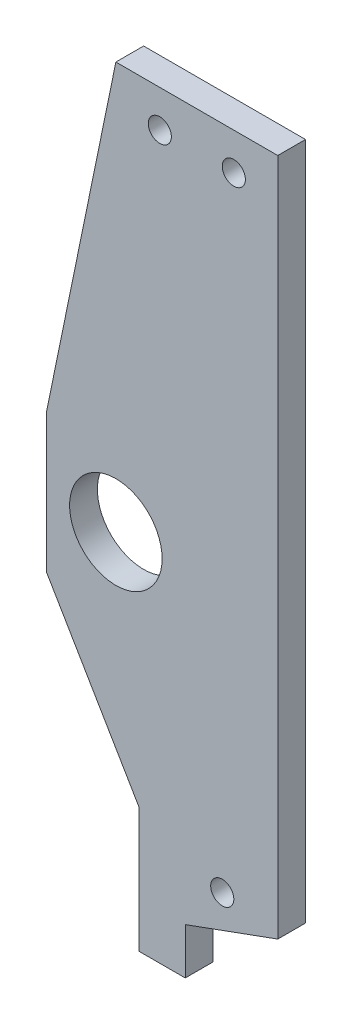
SolidWorks part; units mm, degrees
ref_plane "Front Plane" through (0, 0, 0) normal (0, 0, 1) x (1, 0, 0)
ref_plane "Top Plane" through (0, 0, 0) normal (0, 1, 0) x (1, 0, 0)
ref_plane "Right Plane" through (0, 0, 0) normal (1, 0, 0) x (0, 0, -1)
sketch "Sketch1" plane through (0, 0, 0) normal (0, 0, 1) x (1, 0, 0)
  line L1 (-33.1101, -53.4588) -> (-23.1101, -53.4588)
  line L2 (-33.1101, -53.4588) -> (-33.1101, 23.5412)
  line L3 (-33.1101, 23.5412) -> (-23.1101, 23.5412)
  line L4 (-23.1101, -53.4588) -> (-23.1101, 23.5412)
  dimension "D1" = 77
  dimension "D2" = 10
extrude "Boss-Extrude1" add sketch "Sketch1" along normal blind 3
sketch "Sketch2" plane through (0, 0, 3) normal (0, 0, 1) x (1, 0, 0)
  line L0 (-33.1101, 23.5412) -> (-33.1101, -53.4588) construction
  line L1 (-33.1101, -27.9588) -> (-48.1101, -27.9588)
  line L2 (-33.1101, -27.9588) -> (-33.1101, -12.9588)
  line L3 (-33.1101, -12.9588) -> (-48.1101, -12.9588)
  line L4 (-48.1101, -27.9588) -> (-48.1101, -12.9588)
  line L5 (-33.1101, -53.4588) -> (-23.1101, -53.4588) construction
  dimension "D1" = 25.5
  dimension "D2" = 15
  dimension "D3" = 15
extrude "Boss-Extrude2" add sketch "Sketch2" against normal blind 3
sketch "Sketch3" plane through (0, 0, 3) normal (0, 0, 1) x (1, 0, 0)
  line L0 (-33.1101, 23.5412) -> (-40.6101, 23.5412)
  line L1 (-33.1101, 23.5412) -> (-33.1101, -12.9588)
  line L2 (-33.1101, -12.9588) -> (-48.1101, -12.9588)
  line L3 (-48.1101, -27.9588) -> (-33.1101, -53.4588)
  line L4 (-33.1101, -53.4588) -> (-33.1101, -27.9588)
  line L5 (-33.1101, -27.9588) -> (-48.1101, -27.9588)
  line L6 (-40.6101, 23.5412) -> (-48.1101, -12.9588)
extrude "Boss-Extrude3" add sketch "Sketch3" against normal blind 3
sketch "Sketch4" plane through (0, 0, 3) normal (0, 0, 1) x (1, 0, 0)
  line L0 (-33.1101, -53.4588) -> (-33.1101, -58.4588)
  line L1 (-33.1101, -58.4588) -> (-38.1101, -58.4588)
  line L2 (-38.1101, -58.4588) -> (-38.1101, -44.9588)
  line L4 (-48.1101, -27.9588) -> (-33.1101, -53.4588) construction
  line L5 (-38.1101, -44.9588) -> (-33.1101, -53.4588)
extrude "Boss-Extrude4" add sketch "Sketch4" against normal blind 3
sketch "Sketch5" plane through (0, 0, 3) normal (0, 0, 1) x (1, 0, 0)
  line L0 (-33.1101, -53.4588) -> (-23.1101, -53.4588) construction
  line L3 (-23.1101, 23.5412) -> (-40.6101, 23.5412) construction
  line L4 (-48.1101, -12.9588) -> (-48.1101, -27.9588) construction
  line L11 (-23.1101, 23.5412) -> (-40.6101, 23.5412) construction
  line L12 (-33.1101, -58.4588) -> (-33.1101, -53.4588) construction
  circle A0 centre (-40.6101, -20.4588) radius 5
  circle A1 centre (-29.1101, -48.4588) radius 1.25
  circle A2 centre (-35.8601, 19.5412) radius 1.25
  circle A3 centre (-27.8601, 19.5412) radius 1.25
  point P18 (-31.8601, 23.5412)
  point P21 (-31.8601, 23.5412)
  dimension "D1" = 7.5
  dimension "D3" = 4
  dimension "D5" = 4
  dimension "D2" = 7.5
  dimension "D4" = 4
  dimension "D6" = 4
  dimension "D7" = 4
  dimension "D8" = 5
extrude "Cut-Extrude1" cut sketch "Sketch5" against normal blind 3
sketch "Sketch6" plane through (0, 0, 0) normal (0, 0, -1) x (-1, 0, 0)
  line L0 (23.1101, -53.4588) -> (33.1101, -53.4588)
  line L2 (33.1101, -58.4588) -> (33.1101, -53.4588) construction
  line L4 (33.1101, -53.4588) -> (23.1101, -53.4588) construction
  line L5 (33.1101, -53.4588) -> (23.1101, -49.8171)
  line L6 (23.1101, -53.4588) -> (23.1101, 23.5412) construction
  line L7 (23.1101, -49.8171) -> (23.1101, -53.4588)
  line M5 (23.1101, -53.4588) -> (33.1101, -53.4588)
  line M13 (23.1101, 23.5412) -> (23.1101, -53.4588)
extrude "Cut-Extrude2" cut sketch "Sketch6" against normal blind 10 contours L5 M5 M13
